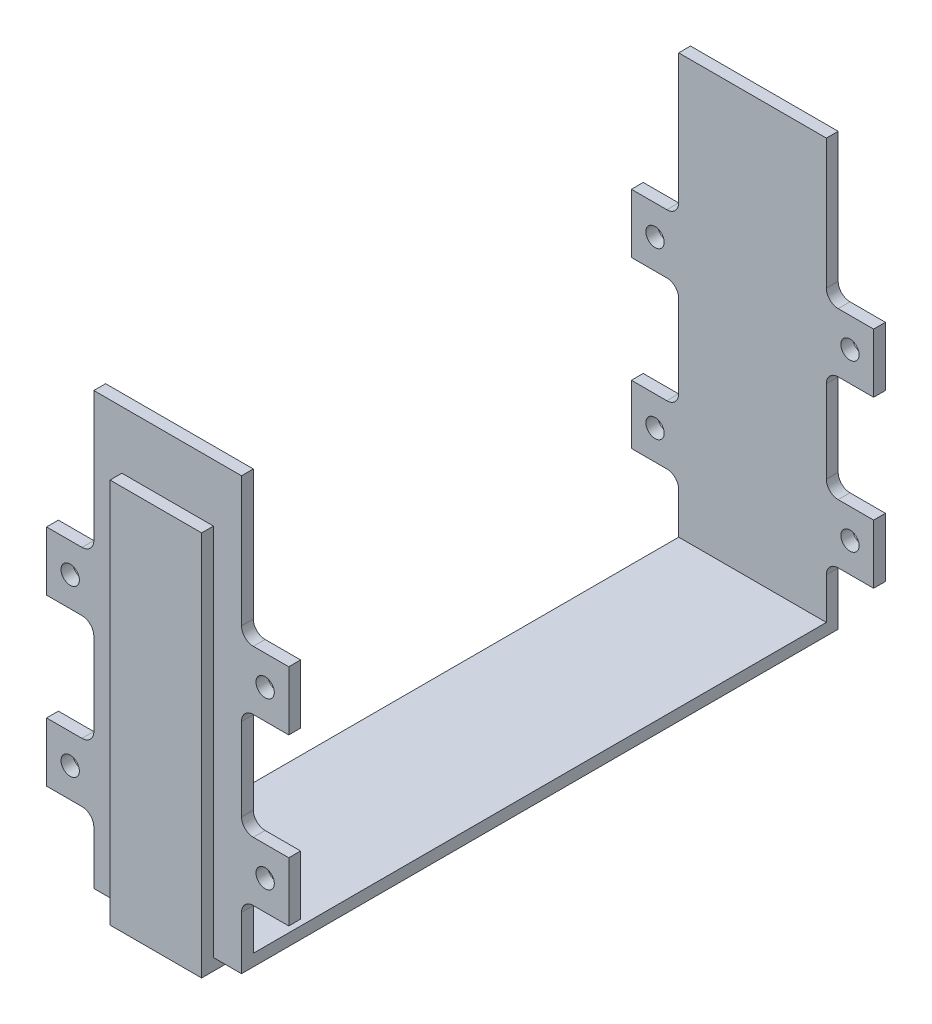
SolidWorks part; units mm, degrees
ref_plane "Front Plane" through (0, 0, 0) normal (0, 0, 1) x (1, 0, 0)
ref_plane "Top Plane" through (0, 0, 0) normal (0, 1, 0) x (1, 0, 0)
ref_plane "Right Plane" through (0, 0, 0) normal (1, 0, 0) x (0, 0, -1)
sketch "Sketch1" plane through (0, 0, 0) normal (1, 0, 0) x (0, 0, -1)
  line L1 (-52.5, 2) -> (52.5, 2)
  line L2 (-52.5, 2) -> (-52.5, -2)
  line L3 (-52.5, -2) -> (52.5, -2)
  line L4 (52.5, 2) -> (52.5, -2)
  line L5 (-52.5, 2) -> (52.5, -2) construction
  line L6 (-52.5, -2) -> (52.5, 2) construction
  line L7 (-52.5, 2) -> (-48.5, 2)
  line L8 (-52.5, 2) -> (-52.5, 63.25)
  line L9 (-52.5, 63.25) -> (-48.5, 63.25)
  line L10 (-48.5, 2) -> (-48.5, 63.25)
  line L11 (-48.5, 63.25) -> (-50.5, 63.25)
  line L12 (-48.5, 63.25) -> (-48.5, 73)
  line L13 (-48.5, 73) -> (-50.5, 73)
  line L14 (-50.5, 63.25) -> (-50.5, 73)
  line L15 (52.5, 2) -> (48.5, 2)
  line L16 (52.5, 2) -> (52.5, 63.25)
  line L17 (52.5, 63.25) -> (48.5, 63.25)
  line L18 (48.5, 2) -> (48.5, 63.25)
  line L19 (48.5, 63.25) -> (50.5, 63.25)
  line L20 (48.5, 63.25) -> (48.5, 73)
  line L21 (48.5, 73) -> (50.5, 73)
  line L22 (50.5, 63.25) -> (50.5, 73)
  point P0 (0, 0)
  dimension "D1" = 105
  dimension "D2" = 4
  dimension "D3" = 4
  dimension "D4" = 61.25
  dimension "D5" = 9.75
  dimension "D6" = 2
  dimension "D7" = 4
  dimension "D8" = 61.25
  dimension "D9" = 2
  dimension "D10" = 9.75
extrude "Boss-Extrude1" add sketch "Sketch1" along normal mid plane 25 contours L4 L1 L2 L3 | L1 L10 L9 L8 | L18 L1 L16 L17 | L12 L11 L14 L13 | L20 L19 L22 L21
sketch "Sketch2" plane through (0, 0, -48.5) normal (0, 0, 1) x (1, 0, 0)
  line L0 (-12.5, 2) -> (-12.5, 73) construction
  line L1 (-12.5, 11) -> (-20.5, 11)
  line L2 (-12.5, 11) -> (-12.5, 21)
  line L3 (-12.5, 21) -> (-20.5, 21)
  line L4 (-20.5, 11) -> (-20.5, 21)
  line L5 (12.5, 2) -> (-12.5, 2) construction
  line L6 (0, 73) -> (0, 13.7024) construction
  line L7 (-12.5, 39) -> (-20.5, 39)
  line L8 (-12.5, 39) -> (-12.5, 49)
  line L9 (-12.5, 49) -> (-20.5, 49)
  line L10 (-20.5, 39) -> (-20.5, 49)
  line L11 (12.5, 73) -> (-12.5, 73) construction
  line L12 (12.5, 21) -> (20.5, 21)
  line L13 (20.5, 11) -> (20.5, 21)
  line L14 (12.5, 11) -> (20.5, 11)
  line L15 (12.5, 11) -> (12.5, 21)
  line L16 (12.5, 49) -> (20.5, 49)
  line L17 (20.5, 39) -> (20.5, 49)
  line L18 (12.5, 39) -> (20.5, 39)
  line L19 (12.5, 39) -> (12.5, 49)
  circle A0 centre (-16.5, 44) radius 1.55
  circle A1 centre (-16.5, 16) radius 1.55
  circle A2 centre (16.5, 16) radius 1.55
  circle A3 centre (16.5, 44) radius 1.55
  dimension "D7" = 3.1
  dimension "D8" = 3.1
  dimension "D9" = 4
  dimension "D1" = 10
  dimension "D2" = 8
  dimension "D3" = 9
  dimension "D4" = 10
  dimension "D5" = 8
  dimension "D6" = 18
extrude "Boss-Extrude2" add sketch "Sketch2" against normal blind 2
sketch "Sketch4" plane through (0, 0, 48.5) normal (0, 0, -1) x (-1, 0, 0)
  line L0 (-12.5, 2) -> (-12.5, 73) construction
  line L1 (-12.5, 11) -> (-20.5, 11)
  line L2 (-12.5, 11) -> (-12.5, 21)
  line L3 (-12.5, 21) -> (-20.5, 21)
  line L4 (-20.5, 11) -> (-20.5, 21)
  line L5 (-12.5, 2) -> (12.5, 2) construction
  line L6 (0, 73) -> (0, 7.87) construction
  line L7 (-12.5, 39) -> (-20.5, 39)
  line L8 (-12.5, 39) -> (-12.5, 49)
  line L9 (-12.5, 49) -> (-20.5, 49)
  line L10 (-20.5, 39) -> (-20.5, 49)
  line L11 (-12.5, 73) -> (12.5, 73) construction
  line L12 (12.5, 21) -> (20.5, 21)
  line L13 (20.5, 11) -> (20.5, 21)
  line L14 (12.5, 11) -> (20.5, 11)
  line L15 (12.5, 11) -> (12.5, 21)
  line L16 (12.5, 49) -> (20.5, 49)
  line L17 (20.5, 39) -> (20.5, 49)
  line L18 (12.5, 39) -> (20.5, 39)
  line L19 (12.5, 39) -> (12.5, 49)
  circle A0 centre (-16.5, 44) radius 1.55
  circle A1 centre (-16.5, 16) radius 1.55
  circle A2 centre (16.5, 16) radius 1.55
  circle A3 centre (16.5, 44) radius 1.55
  dimension "D7" = 3.1
  dimension "D8" = 3.1
  dimension "D1" = 8
  dimension "D2" = 10
  dimension "D3" = 9
  dimension "D4" = 8
  dimension "D5" = 10
  dimension "D6" = 18
extrude "Boss-Extrude3" add sketch "Sketch4" against normal blind 2
sketch "Sketch5" plane through (-12.5, 0, 0) normal (-1, 0, 0) x (0, 0, 1)
  line L0 (52.5, -2) -> (-52.5, -2) construction
  line L1 (-52.5, 63.25) -> (-50.5, 63.25)
  line L2 (-52.5, 63.25) -> (-52.5, -2)
  line L3 (-52.5, -2) -> (-50.5, -2)
  line L4 (-50.5, 63.25) -> (-50.5, -2)
  line L6 (52.5, 63.25) -> (50.5, 63.25)
  line L7 (52.5, 63.25) -> (52.5, -2)
  line L8 (52.5, -2) -> (50.5, -2)
  line L9 (50.5, 63.25) -> (50.5, -2)
  line L10 (-50.5, -2) -> (50.5, -2)
  line L11 (-50.5, -2) -> (-50.5, 0)
  line L12 (-50.5, 0) -> (50.5, 0)
  line L13 (50.5, -2) -> (50.5, 0)
  line M7 (50.5, 49) -> (50.5, 39)
  line M11 (50.5, 21) -> (50.5, 11)
  line M17 (-50.5, 11) -> (-50.5, 21)
  line M21 (-50.5, 39) -> (-50.5, 49)
  line M26 (-50.5, 63.25) -> (-52.5, 63.25)
  line M27 (-52.5, 63.25) -> (-52.5, -2)
  line M28 (-52.5, -2) -> (52.5, -2)
  line M29 (52.5, -2) -> (52.5, 63.25)
  line M30 (52.5, 63.25) -> (50.5, 63.25)
  dimension "D1" = 2
  dimension "D2" = 2
  dimension "D3" = 2
extrude "Cut-Extrude1" cut sketch "Sketch5" against normal blind 4.75 contours L4 M26 M27 M28 M17 M21 | L12 L4 L9 M28 | L9 M30 M7 M11 M28 M29
sketch "Sketch6" plane through (12.5, 0, 0) normal (1, 0, 0) x (0, 0, -1)
  line L1 (-50.5, 63.25) -> (-52.5, 63.25)
  line L2 (-50.5, 63.25) -> (-50.5, -2)
  line L3 (-50.5, -2) -> (-52.5, -2)
  line L4 (-52.5, 63.25) -> (-52.5, -2)
  line L5 (50.5, 63.25) -> (52.5, 63.25)
  line L6 (50.5, 63.25) -> (50.5, -2)
  line L7 (50.5, -2) -> (52.5, -2)
  line L8 (52.5, 63.25) -> (52.5, -2)
  line L9 (-50.5, -2) -> (50.5, -2)
  line L10 (-50.5, -2) -> (-50.5, 0)
  line L11 (-50.5, 0) -> (50.5, 0)
  line L12 (50.5, -2) -> (50.5, 0)
  line M15 (-52.5, -2) -> (52.5, -2)
  dimension "D1" = 2
extrude "Cut-Extrude2" cut sketch "Sketch6" against normal blind 4.75 contours L11 L2 L6 M15
fillet "Fillet1" radius 2 16 edges at (12.5, 21, 49.5) (12.5, 11, 49.5) (12.5, 49, 49.5) (12.5, 39, 49.5) (-12.5, 11, 49.5) (-12.5, 21, 49.5) (-12.5, 39, 49.5) (-12.5, 49, 49.5) (-12.5, 21, -49.5) (-12.5, 11, -49.5) (-12.5, 49, -49.5) (-12.5, 39, -49.5) (12.5, 11, -49.5) (12.5, 21, -49.5) (12.5, 39, -49.5) (12.5, 49, -49.5)
